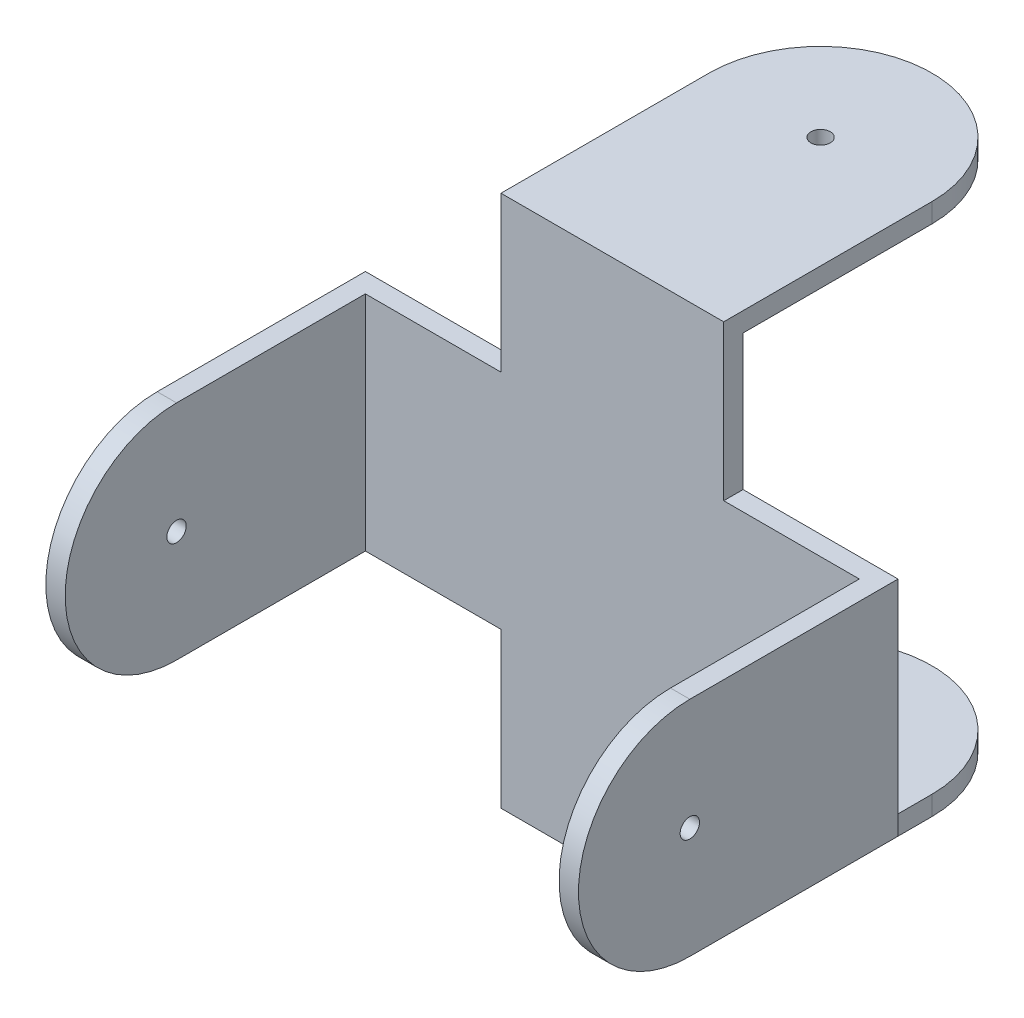
SolidWorks part; units mm, degrees
ref_plane "前视基准面" through (0, 0, 0) normal (0, 0, 1) x (1, 0, 0)
ref_plane "上视基准面" through (0, 0, 0) normal (0, 1, 0) x (1, 0, 0)
ref_plane "右视基准面" through (0, 0, 0) normal (1, 0, 0) x (0, 0, -1)
sketch "草图1" plane through (0, 0, 0) normal (0, 0, 1) x (1, 0, 0)
  line L0 (27.5, -11.5) -> (27.5, 11.5)
  line L1 (-11.5, -27.5) -> (11.5, -27.5)
  line L2 (-11.5, -27.5) -> (-11.5, -11.5)
  line L3 (-11.5, 27.5) -> (11.5, 27.5)
  line L4 (11.5, -27.5) -> (11.5, -11.5)
  line L5 (-11.5, -27.5) -> (11.5, 27.5) construction
  line L6 (-11.5, 27.5) -> (11.5, -27.5) construction
  line L7 (27.5, -11.5) -> (11.5, -11.5)
  line L8 (-27.5, -11.5) -> (-27.5, 11.5)
  line L9 (27.5, 11.5) -> (11.5, 11.5)
  line L10 (27.5, -11.5) -> (-27.5, 11.5) construction
  line L11 (-27.5, -11.5) -> (0, 0) construction
  line L12 (11.5, 11.5) -> (11.5, 27.5)
  line L13 (0, 0) -> (27.5, 11.5) construction
  line L14 (-11.5, 11.5) -> (-11.5, 27.5)
  line L15 (-11.5, 11.5) -> (-27.5, 11.5)
  line L16 (-11.5, -11.5) -> (-27.5, -11.5)
  point P0 (0, 0)
  point P6 (0, 0)
  point P11 (0, 0)
  point P12 (0, 0)
  point P13 (0, 0)
  point P14 (0, 0)
  point P15 (0.8166, 0)
extrude "凸台-拉伸1" add sketch "草图1" along normal blind 2
sketch "草图3" plane through (0, 27.5, 0) normal (0, 1, 0) x (1, 0, 0)
  line L1 (-11.5, -2) -> (11.5, -2)
  line L2 (-11.5, -2) -> (-11.5, 19.5)
  line L4 (11.5, -2) -> (11.5, 19.5)
  arc A0 (11.5, 19.5) -> (-11.5, 19.5) centre (0, 19.5) ccw
  point P1 (0, 0)
extrude "凸台-拉伸2" add sketch "草图3" against normal blind 2
sketch "草图4" plane through (0, 27.5, 0) normal (0, 1, 0) x (1, 0, 0)
  circle A0 centre (0, 19.5) radius 1
extrude "切除-拉伸1" cut sketch "草图4" against normal up to next (2 mm away)
mirror "镜向2" about plane through (0, 0, 0) normal (0, 1, 0) of "切除-拉伸1", "凸台-拉伸2"
sketch "草图7" plane through (-27.5, 0, 0) normal (-1, 0, 0) x (0, 0, 1)
  line L1 (0, 11.5) -> (21.5, 11.5)
  line L2 (0, 11.5) -> (0, -11.5)
  line L3 (0, -11.5) -> (21.5, -11.5)
  arc A0 (21.5, -11.5) -> (21.5, 11.5) centre (21.5, 0) ccw
extrude "凸台-拉伸4" add sketch "草图7" against normal blind 2
sketch "草图8" plane through (-27.5, 0, 0) normal (-1, 0, 0) x (0, 0, 1)
  circle A0 centre (21.5, 0) radius 1
extrude "切除-拉伸3" cut sketch "草图8" against normal up to next (2 mm away)
mirror "镜向4" about plane through (0, 0, 0) normal (1, 0, 0) of "切除-拉伸3", "凸台-拉伸4"
